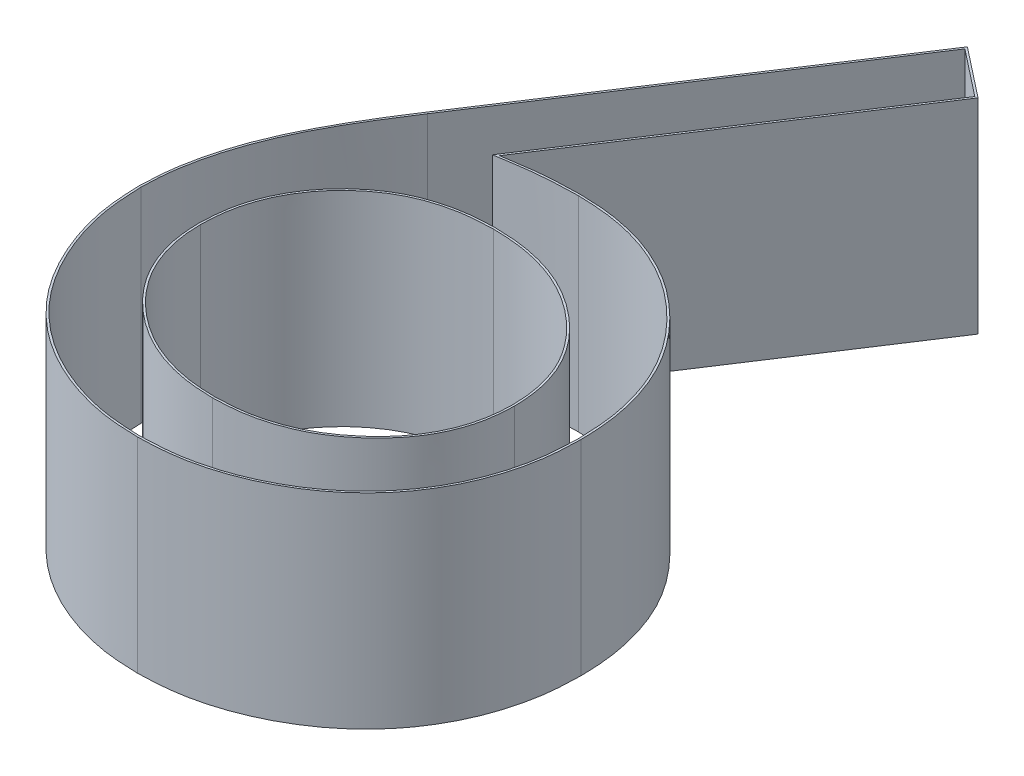
SolidWorks part; units mm, degrees
ref_plane "Front Plane" through (0, 0, 0) normal (0, 0, 1) x (1, 0, 0)
ref_plane "Top Plane" through (0, 0, 0) normal (0, 1, 0) x (1, 0, 0)
ref_plane "Right Plane" through (0, 0, 0) normal (1, 0, 0) x (0, 0, -1)
sketch "Sketch1" plane through (0, 0, 0) normal (0, 1, 0) x (1, 0, 0)
  text T0 "6"
extrude "Boss-Extrude1" add sketch "Sketch1" along normal blind 1
sketch "Sketch2" plane through (0, 1, 0) normal (0, 1, 0) x (1, 0, 0)
  line L6 (1.7524, 3.5751) -> (0.7137, 1.9871)
  line L7 (1.0464, 1.9721) -> (1.9785, 3.3975)
  line L8 (1.9785, 3.3975) -> (1.7524, 3.5751)
  line L9 (1.7524, 3.5751) -> (0.7137, 1.9871)
  line L10 (1.0464, 1.9721) -> (1.9785, 3.3975)
  line L11 (1.9785, 3.3975) -> (1.7524, 3.5751)
  spline S10 degree 3 poles (-3621.8039, 1697.738) (85.0177, -19.1975) (4.2377, 10.5214) (0.4074, 1.4221) (0.3778, 1.3357) (0.3468, 1.2032) (0.3384, 1.1586) (-0.2453, -3.6198) (40.4082, -17.4873) (-3907.8217, 852.3184) knots -26.044016 -26.044016 -26.044016 -26.044016 0.5 0.5 0.75 0.75 0.875 0.875 13.957095 13.957095 13.957095 13.957095 only from (0.7137, 1.9871) to (0.3241, 0.976)
  spline S11 degree 3 poles (-3933.2533, -724.0518) (55.5273, 22.2972) (-0.6641, 6.1427) (0.3557, 0.7033) (0.3757, 0.6372) (0.4536, 0.4434) (0.5261, 0.3263) (0.7217, 0.1272) (0.839, 0.0505) (1.0316, -0.0277) (1.0977, -0.0476) (6.4728, -1.086) (25.4473, 56.4368) (-1248.3773, -3799.5694) knots -9.853719 -9.853719 -9.853719 -9.853719 0.125 0.125 0.25 0.25 0.5 0.5 0.75 0.75 0.875 0.875 10.611952 10.611952 10.611952 10.611952 only from (0.3241, 0.976) to (1.3742, -0.0797)
  spline S12 degree 3 poles (701.3786, -3938.0577) (-19.8922, 55.8559) (-3.8818, -1.0698) (1.653, -0.0483) (1.7208, -0.0288) (1.9194, 0.049) (2.0393, 0.1227) (2.2459, 0.3185) (2.3264, 0.4365) (2.4066, 0.6329) (2.4261, 0.7004) (3.4598, 6.1319) (-54.5186, 25.0372) (3808.0775, -1230.0112) knots -9.802401 -9.802401 -9.802401 -9.802401 0.125 0.125 0.25 0.25 0.5 0.5 0.75 0.75 0.875 0.875 10.52539 10.52539 10.52539 10.52539 only from (1.3742, -0.0797) to (2.4579, 0.9823)
  spline S13 degree 3 poles (3949.0814, 651.2393) (-56.4276, -20.3337) (3.46, -4.4252) (2.4285, 1.2496) (2.4099, 1.3151) (2.3343, 1.504) (2.2565, 1.6155) (2.1127, 1.7585) (2.0612, 1.8018) (1.9495, 1.8777) (1.8887, 1.9096) (1.7643, 1.9606) (1.6996, 1.979) (-4.2379, 3.0622) (-18.6435, -59.289) (726.0372, 3935.6575) knots -10.491801 -10.491801 -10.491801 -10.491801 0.125 0.125 0.25 0.25 0.5 0.5 0.625 0.625 0.75 0.75 0.875 0.875 11.836094 11.836094 11.836094 11.836094 only from (2.4579, 0.9823) to (1.4296, 2.0092)
  spline S14 degree 3 poles (-165.1905, 3998.4231) (14.2339, -18.0017) (7.3718, 2.267) (1.3381, 2.0063) (1.3076, 2.005) (1.2771, 2.0032) (1.2132, 1.9971) (1.1797, 1.9927) (1.1464, 1.9878) (-5.2153, 1.0518) (-8.9031, -17.6658) (-604.8895, 3955.5907) knots -0.018027 -0.018027 -0.018027 -0.018027 0.000092 0.000092 0.000092 0.000183 0.000183 0.000284 0.000284 0.000284 0.019575 0.019575 0.019575 0.019575 only from (1.4296, 2.0092) to (1.0464, 1.9721)
  spline S15 degree 3 poles (0.7137, 1.9871) (0.6134, 1.8329) (0.5146, 1.6768) (0.4074, 1.4221) (0.3778, 1.3357) (0.3468, 1.2032) (0.3384, 1.1586) (0.3274, 1.0682) (0.3256, 1.0221) (0.3241, 0.976) knots 0 0 0 0 0.5 0.5 0.75 0.75 0.875 0.875 1 1 1 1
  spline S16 degree 3 poles (0.3241, 0.976) (0.3268, 0.9068) (0.3305, 0.8378) (0.3557, 0.7033) (0.3757, 0.6372) (0.4536, 0.4434) (0.5261, 0.3263) (0.7217, 0.1272) (0.839, 0.0505) (1.0316, -0.0277) (1.0977, -0.0476) (1.2339, -0.074) (1.3043, -0.0775) (1.3742, -0.0797) knots 0 0 0 0 0.125 0.125 0.25 0.25 0.5 0.5 0.75 0.75 0.875 0.875 1 1 1 1
  spline S17 degree 3 poles (1.3742, -0.0797) (1.4449, -0.0772) (1.5154, -0.0737) (1.653, -0.0483) (1.7208, -0.0288) (1.9194, 0.049) (2.0393, 0.1227) (2.2459, 0.3185) (2.3264, 0.4365) (2.4066, 0.6329) (2.4261, 0.7004) (2.4526, 0.8394) (2.4559, 0.9111) (2.4579, 0.9823) knots 0 0 0 0 0.125 0.125 0.25 0.25 0.5 0.5 0.75 0.75 0.875 0.875 1 1 1 1
  spline S18 degree 3 poles (2.4579, 0.9823) (2.4561, 1.05) (2.4525, 1.1175) (2.4285, 1.2496) (2.4099, 1.3151) (2.3343, 1.504) (2.2565, 1.6155) (2.1127, 1.7585) (2.0612, 1.8018) (1.9495, 1.8777) (1.8887, 1.9096) (1.7643, 1.9606) (1.6996, 1.979) (1.5657, 2.0034) (1.4976, 2.0074) (1.4296, 2.0092) knots 0 0 0 0 0.125 0.125 0.25 0.25 0.5 0.5 0.625 0.625 0.75 0.75 0.875 0.875 1 1 1 1
  spline S19 degree 3 poles (1.4296, 2.0092) (1.3991, 2.0084) (1.3686, 2.0076) (1.3076, 2.005) (1.2771, 2.0032) (1.2132, 1.9971) (1.1797, 1.9927) (1.113, 1.9829) (1.0797, 1.9775) (1.0464, 1.9721) knots 0 0 0 0 0.000092 0.000092 0.000183 0.000183 0.000284 0.000284 0.000385 0.000385 0.000385 0.000385
  spline S29 degree 3 poles (-3939.5958, -686.6182) (62.8588, 21.5634) (-0.3713, 5.4699) (0.6434, 0.7723) (0.6597, 0.7258) (0.7213, 0.5938) (0.7843, 0.5173) (0.9303, 0.3904) (1.015, 0.3395) (1.1508, 0.2907) (1.198, 0.2782) (5.8476, -0.4644) (15.5483, 48.9526) (-389.4491, -3980.3211) knots -12.224404 -12.224404 -12.224404 -12.224404 0.125 0.125 0.25 0.25 0.5 0.5 0.75 0.75 0.875 0.875 12.871208 12.871208 12.871208 12.871208 only from (0.6182, 0.9634) to (1.391, 0.2592)
  spline S30 degree 3 poles (780.1284, -3923.1171) (-17.7074, 48.5533) (-3.0591, -0.4629) (1.5835, 0.2781) (1.6301, 0.2903) (1.7216, 0.3232) (1.7667, 0.3437) (1.8494, 0.3936) (1.8879, 0.4224) (1.9975, 0.5176) (2.0597, 0.5942) (2.1226, 0.7252) (2.1385, 0.7721) (3.1523, 5.4448) (-59.8985, 21.5268) (3941.8981, -689.4134) knots -11.957369 -11.957369 -11.957369 -11.957369 0.125 0.125 0.25 0.25 0.375 0.375 0.5 0.5 0.75 0.75 0.875 0.875 13.145545 13.145545 13.145545 13.145545 only from (1.391, 0.2592) to (2.1638, 0.9633)
  spline S31 degree 3 poles (3948.9547, 650.3809) (-70.8629, -21.9988) (3.31, -4.0929) (2.1368, 1.159) (2.1205, 1.2069) (2.0534, 1.3389) (1.9876, 1.4162) (1.8362, 1.5419) (1.749, 1.5932) (1.6091, 1.6399) (1.5607, 1.6518) (-3.099, 2.3647) (-12.4073, -45.6549) (371.4479, 3984.3305) knots -13.357508 -13.357508 -13.357508 -13.357508 0.125 0.125 0.25 0.25 0.5 0.5 0.75 0.75 0.875 0.875 12.644254 12.644254 12.644254 12.644254 only from (2.1638, 0.9633) to (1.3637, 1.6703)
  spline S32 degree 3 poles (-675.3849, 3943.7117) (18.467, -44.3458) (5.6966, 2.3377) (1.1739, 1.6527) (1.1277, 1.6413) (0.9913, 1.5948) (0.9086, 1.5427) (0.7683, 1.4109) (0.7112, 1.3312) (0.6547, 1.2) (0.6406, 1.1546) (-0.1926, -3.1595) (52.0383, -17.8489) (-3849.31, 1085.7411) knots -11.789149 -11.789149 -11.789149 -11.789149 0.125 0.125 0.25 0.25 0.5 0.5 0.75 0.75 0.875 0.875 12.169586 12.169586 12.169586 12.169586 only from (1.3637, 1.6703) to (0.6182, 0.9634)
  spline S33 degree 3 poles (0.6182, 0.9634) (0.6195, 0.9147) (0.6231, 0.8665) (0.6434, 0.7723) (0.6597, 0.7258) (0.7213, 0.5938) (0.7843, 0.5173) (0.9303, 0.3904) (1.015, 0.3395) (1.1508, 0.2907) (1.198, 0.2782) (1.2939, 0.2629) (1.3424, 0.2607) (1.391, 0.2592) knots 0 0 0 0 0.125 0.125 0.25 0.25 0.5 0.5 0.75 0.75 0.875 0.875 1 1 1 1
  spline S34 degree 3 poles (1.391, 0.2592) (1.4398, 0.2607) (1.4884, 0.2629) (1.5835, 0.2781) (1.6301, 0.2903) (1.7216, 0.3232) (1.7667, 0.3437) (1.8494, 0.3936) (1.8879, 0.4224) (1.9975, 0.5176) (2.0597, 0.5942) (2.1226, 0.7252) (2.1385, 0.7721) (2.159, 0.8663) (2.1626, 0.9146) (2.1638, 0.9633) knots 0 0 0 0 0.125 0.125 0.25 0.25 0.375 0.375 0.5 0.5 0.75 0.75 0.875 0.875 1 1 1 1
  spline S35 degree 3 poles (2.1638, 0.9633) (2.1627, 1.0132) (2.1584, 1.0625) (2.1368, 1.159) (2.1205, 1.2069) (2.0534, 1.3389) (1.9876, 1.4162) (1.8362, 1.5419) (1.749, 1.5932) (1.6091, 1.6399) (1.5607, 1.6518) (1.4627, 1.6668) (1.4132, 1.6688) (1.3637, 1.6703) knots 0 0 0 0 0.125 0.125 0.25 0.25 0.5 0.5 0.75 0.75 0.875 0.875 1 1 1 1
  spline S36 degree 3 poles (1.3637, 1.6703) (1.3157, 1.6689) (1.2679, 1.667) (1.1739, 1.6527) (1.1277, 1.6413) (0.9913, 1.5948) (0.9086, 1.5427) (0.7683, 1.4109) (0.7112, 1.3312) (0.6547, 1.2) (0.6406, 1.1546) (0.6224, 1.0601) (0.6198, 1.0116) (0.6182, 0.9634) knots 0 0 0 0 0.125 0.125 0.25 0.25 0.5 0.5 0.75 0.75 0.875 0.875 1 1 1 1
  dimension "D1" = 0.01
  dimension "D2" = 0.01
extrude "Cut-Extrude1" cut sketch "Sketch2" against normal blind 1
